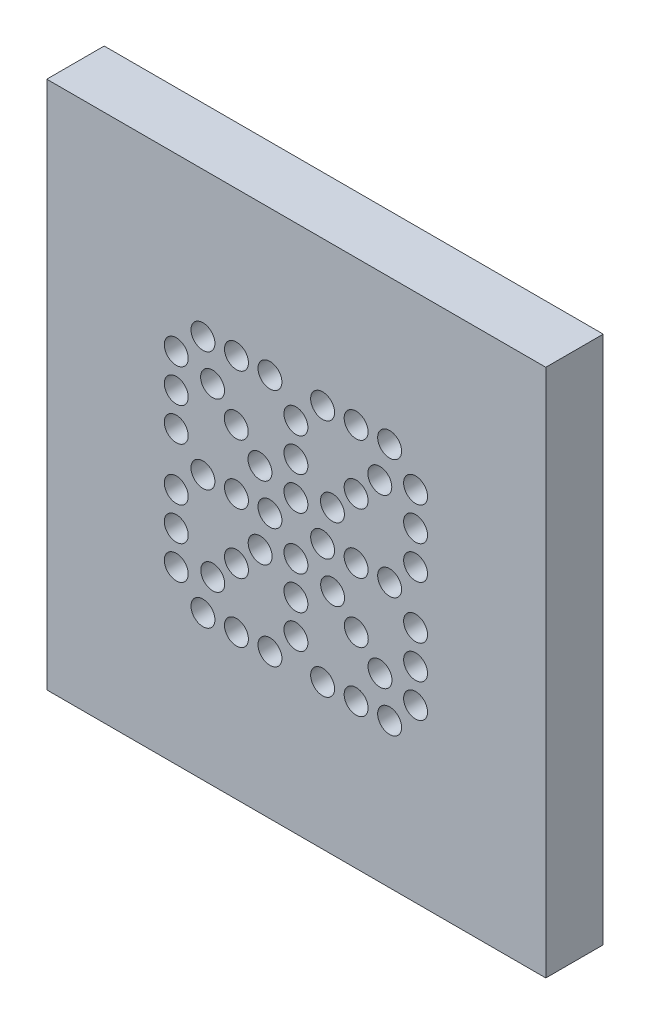
SolidWorks part; units mm, degrees
material "ABS PC"
ref_plane "Front Plane" through (0, 0, 0) normal (0, 0, 1) x (1, 0, 0)
ref_plane "Top Plane" through (0, 0, 0) normal (0, 1, 0) x (1, 0, 0)
ref_plane "Right Plane" through (0, 0, 0) normal (1, 0, 0) x (0, 0, -1)
sketch "Sketch1" plane through (0, 0, 0) normal (0, 0, 1) x (1, 0, 0)
  line L0 (265.9975, 197.0179) -> (342.1693, 194.9479) construction
  line L1 (297.418, 228.3826) -> (298.307, 228.3826) construction
  line L2 (297.418, 228.3826) -> (300.593, 228.3826) construction
  line L3 (302.371, 228.3826) -> (302.371, 231.5576) construction
  line L4 (296.7097, 229.0811) -> (296.7097, 229.9701) construction
  line L5 (296.7097, 230.8591) -> (296.7097, 234.0341) construction
  line L6 (296.7097, 234.0341) -> (299.8847, 234.0341) construction
  line L7 (296.7097, 234.0341) -> (297.0639, 234.3834) construction
  line L8 (296.7097, 234.0341) -> (297.418, 234.7326) construction
  line L9 (299.196, 231.5576) -> (300.593, 231.5576) construction
  line L10 (297.0639, 234.3834) -> (299.5404, 231.9069) construction
  line L11 (296.7097, 232.2561) -> (296.7097, 230.8591)
  line L12 (297.418, 231.5576) -> (296.7097, 231.5576) construction
  line L13 (299.8847, 232.2561) -> (299.196, 231.5576) construction
  line L14 (299.8945, 231.5576) -> (298.9307, 232.5165) construction
  line L15 (299.8945, 231.5576) -> (300.8534, 232.5214) construction
  line L16 (297.418, 234.7326) -> (307.578, 234.7326) construction
  line L17 (293.5347, 230.4146) -> (293.5347, 229.5256) construction
  line L18 (293.5347, 232.7006) -> (293.5347, 230.4146) construction
  line L19 (335.8892, 225.6039) -> (291.1852, 225.6039)
  line L20 (335.8892, 225.6039) -> (335.8892, 237.5114)
  line L21 (335.8892, 237.5114) -> (291.1852, 237.5114)
  line L22 (291.1852, 225.6039) -> (291.1852, 237.5114)
  line L23 (335.8892, 225.6039) -> (291.1852, 237.5114) construction
  line L24 (335.8892, 237.5114) -> (291.1852, 225.6039) construction
  line L25 (333.5397, 232.2561) -> (333.5397, 230.8591) construction
  line L26 (293.5347, 231.5576) -> (333.5397, 231.5576) construction
  circle A0 centre (297.418, 228.3826) radius 0.3175
  circle A3 centre (298.307, 228.3826) radius 0.3175
  circle A4 centre (299.196, 228.3826) radius 0.3175
  circle A5 centre (300.593, 228.3826) radius 0.3175
  circle A6 centre (301.482, 228.3826) radius 0.3175
  circle A7 centre (302.371, 228.3826) radius 0.3175
  circle A8 centre (302.371, 231.5576) radius 0.3175
  circle A9 centre (301.482, 231.5576) radius 0.3175
  circle A10 centre (300.593, 231.5576) radius 0.3175
  circle A11 centre (299.196, 231.5576) radius 0.3175
  circle A12 centre (298.307, 231.5576) radius 0.3175
  circle A13 centre (297.418, 231.5576) radius 0.3175
  circle A14 centre (302.371, 234.7326) radius 0.3175
  circle A15 centre (301.482, 234.7326) radius 0.3175
  circle A16 centre (300.593, 234.7326) radius 0.3175
  circle A17 centre (299.196, 234.7326) radius 0.3175
  circle A18 centre (298.307, 234.7326) radius 0.3175
  circle A19 centre (297.418, 234.7326) radius 0.3175
  circle A20 centre (296.7097, 229.0811) radius 0.3175
  circle A21 centre (296.7097, 229.9701) radius 0.3175
  circle A22 centre (296.7097, 230.8591) radius 0.3175
  circle A23 centre (296.7097, 234.0341) radius 0.3175
  circle A24 centre (296.7097, 233.1451) radius 0.3175
  circle A25 centre (296.7097, 232.2561) radius 0.3175
  circle A26 centre (299.8847, 234.0341) radius 0.3175
  circle A27 centre (299.8847, 233.1451) radius 0.3175
  circle A28 centre (299.8847, 232.2561) radius 0.3175
  circle A29 centre (299.8847, 230.8591) radius 0.3175
  circle A30 centre (299.8847, 229.9701) radius 0.3175
  circle A31 centre (299.8847, 229.0811) radius 0.3175
  circle A32 centre (297.6735, 233.7737) radius 0.3175
  circle A33 centre (298.3021, 233.1451) radius 0.3175
  circle A34 centre (298.9307, 232.5165) radius 0.3175
  circle A35 centre (303.0597, 234.0341) radius 0.3175
  circle A36 centre (303.0597, 233.1451) radius 0.3175
  circle A37 centre (303.0597, 232.2561) radius 0.3175
  circle A38 centre (303.0597, 230.8591) radius 0.3175
  circle A39 centre (303.0597, 229.9701) radius 0.3175
  circle A40 centre (303.0597, 229.0811) radius 0.3175
  circle A41 centre (300.8534, 232.5214) radius 0.3175
  circle A42 centre (301.482, 233.15) radius 0.3175
  circle A43 centre (302.1106, 233.7786) radius 0.3175
  circle A44 centre (300.8582, 230.5987) radius 0.3175
  circle A45 centre (301.4869, 229.9701) radius 0.3175
  circle A46 centre (302.1155, 229.3415) radius 0.3175
  circle A47 centre (298.9356, 230.5939) radius 0.3175
  circle A48 centre (298.307, 229.9653) radius 0.3175
  circle A49 centre (297.6784, 229.3366) radius 0.3175
  circle A50 centre (307.578, 234.7326) radius 0.3175
  circle A51 centre (306.8697, 234.0341) radius 0.3175
  circle A52 centre (306.8697, 233.1451) radius 0.3175
  circle A53 centre (306.8697, 232.2561) radius 0.3175
  circle A54 centre (308.467, 234.7326) radius 0.3175
  circle A55 centre (309.356, 234.7326) radius 0.3175
  circle A56 centre (310.753, 234.7326) radius 0.3175
  circle A57 centre (311.642, 234.7326) radius 0.3175
  circle A58 centre (312.531, 234.7326) radius 0.3175
  circle A59 centre (313.2197, 234.0341) radius 0.3175
  circle A60 centre (313.2197, 233.1451) radius 0.3175
  circle A61 centre (313.2197, 232.2561) radius 0.3175
  circle A62 centre (313.2197, 230.8591) radius 0.3175
  circle A63 centre (313.2197, 229.9701) radius 0.3175
  circle A64 centre (313.2197, 229.0811) radius 0.3175
  circle A65 centre (312.531, 228.3826) radius 0.3175
  circle A66 centre (311.642, 228.3826) radius 0.3175
  circle A67 centre (310.753, 228.3826) radius 0.3175
  circle A68 centre (309.356, 228.3826) radius 0.3175
  circle A69 centre (308.467, 228.3826) radius 0.3175
  circle A70 centre (307.578, 228.3826) radius 0.3175
  circle A71 centre (306.8697, 229.0811) radius 0.3175
  circle A72 centre (306.8697, 229.9701) radius 0.3175
  circle A73 centre (306.8697, 230.8591) radius 0.3175
  circle A74 centre (307.578, 231.5576) radius 0.3175
  circle A75 centre (308.467, 231.5576) radius 0.3175
  circle A76 centre (309.356, 231.5576) radius 0.3175
  circle A77 centre (310.753, 231.5576) radius 0.3175
  circle A78 centre (311.642, 231.5576) radius 0.3175
  circle A79 centre (312.531, 231.5576) radius 0.3175
  circle A80 centre (312.2706, 233.7786) radius 0.3175
  circle A81 centre (311.642, 233.15) radius 0.3175
  circle A82 centre (311.0134, 232.5214) radius 0.3175
  circle A83 centre (310.0447, 232.2561) radius 0.3175
  circle A84 centre (310.0447, 233.1451) radius 0.3175
  circle A85 centre (310.0447, 234.0341) radius 0.3175
  circle A86 centre (309.0907, 232.5165) radius 0.3175
  circle A87 centre (308.4621, 233.1451) radius 0.3175
  circle A88 centre (307.8335, 233.7737) radius 0.3175
  circle A89 centre (307.8384, 229.3366) radius 0.3175
  circle A90 centre (308.467, 229.9653) radius 0.3175
  circle A91 centre (309.0956, 230.5939) radius 0.3175
  circle A92 centre (310.0447, 230.8591) radius 0.3175
  circle A93 centre (310.0447, 229.9701) radius 0.3175
  circle A94 centre (310.0447, 229.0811) radius 0.3175
  circle A95 centre (312.2755, 229.3415) radius 0.3175
  circle A96 centre (311.6469, 229.9701) radius 0.3175
  circle A97 centre (311.0182, 230.5987) radius 0.3175
  circle A98 centre (317.738, 234.7326) radius 0.3175
  circle A99 centre (317.0297, 234.0341) radius 0.3175
  circle A100 centre (317.0297, 233.1451) radius 0.3175
  circle A101 centre (317.0297, 232.2561) radius 0.3175
  circle A102 centre (318.627, 234.7326) radius 0.3175
  circle A103 centre (319.516, 234.7326) radius 0.3175
  circle A104 centre (320.913, 234.7326) radius 0.3175
  circle A105 centre (321.802, 234.7326) radius 0.3175
  circle A106 centre (322.691, 234.7326) radius 0.3175
  circle A107 centre (323.3797, 234.0341) radius 0.3175
  circle A108 centre (323.3797, 233.1451) radius 0.3175
  circle A109 centre (323.3797, 232.2561) radius 0.3175
  circle A110 centre (323.3797, 230.8591) radius 0.3175
  circle A111 centre (323.3797, 229.9701) radius 0.3175
  circle A112 centre (323.3797, 229.0811) radius 0.3175
  circle A113 centre (322.691, 228.3826) radius 0.3175
  circle A114 centre (321.802, 228.3826) radius 0.3175
  circle A115 centre (320.913, 228.3826) radius 0.3175
  circle A116 centre (319.516, 228.3826) radius 0.3175
  circle A117 centre (318.627, 228.3826) radius 0.3175
  circle A118 centre (317.738, 228.3826) radius 0.3175
  circle A119 centre (317.0297, 229.0811) radius 0.3175
  circle A120 centre (317.0297, 229.9701) radius 0.3175
  circle A121 centre (317.0297, 230.8591) radius 0.3175
  circle A122 centre (317.738, 231.5576) radius 0.3175
  circle A123 centre (318.627, 231.5576) radius 0.3175
  circle A124 centre (319.516, 231.5576) radius 0.3175
  circle A125 centre (320.913, 231.5576) radius 0.3175
  circle A126 centre (321.802, 231.5576) radius 0.3175
  circle A127 centre (322.691, 231.5576) radius 0.3175
  circle A128 centre (322.4306, 233.7786) radius 0.3175
  circle A129 centre (321.802, 233.15) radius 0.3175
  circle A130 centre (321.1734, 232.5214) radius 0.3175
  circle A131 centre (320.2047, 232.2561) radius 0.3175
  circle A132 centre (320.2047, 233.1451) radius 0.3175
  circle A133 centre (320.2047, 234.0341) radius 0.3175
  circle A134 centre (319.2507, 232.5165) radius 0.3175
  circle A135 centre (318.6221, 233.1451) radius 0.3175
  circle A136 centre (317.9935, 233.7737) radius 0.3175
  circle A137 centre (317.9984, 229.3366) radius 0.3175
  circle A138 centre (318.627, 229.9653) radius 0.3175
  circle A139 centre (319.2556, 230.5939) radius 0.3175
  circle A140 centre (320.2047, 230.8591) radius 0.3175
  circle A141 centre (320.2047, 229.9701) radius 0.3175
  circle A142 centre (320.2047, 229.0811) radius 0.3175
  circle A143 centre (322.4355, 229.3415) radius 0.3175
  circle A144 centre (321.8069, 229.9701) radius 0.3175
  circle A145 centre (321.1782, 230.5987) radius 0.3175
  circle A146 centre (327.898, 234.7326) radius 0.3175
  circle A147 centre (327.1897, 234.0341) radius 0.3175
  circle A148 centre (327.1897, 233.1451) radius 0.3175
  circle A149 centre (327.1897, 232.2561) radius 0.3175
  circle A150 centre (328.787, 234.7326) radius 0.3175
  circle A151 centre (329.676, 234.7326) radius 0.3175
  circle A152 centre (331.073, 234.7326) radius 0.3175
  circle A153 centre (331.962, 234.7326) radius 0.3175
  circle A154 centre (332.851, 234.7326) radius 0.3175
  circle A155 centre (333.5397, 234.0341) radius 0.3175
  circle A156 centre (333.5397, 233.1451) radius 0.3175
  circle A157 centre (333.5397, 232.2561) radius 0.3175
  circle A158 centre (333.5397, 230.8591) radius 0.3175
  circle A159 centre (333.5397, 229.9701) radius 0.3175
  circle A160 centre (333.5397, 229.0811) radius 0.3175
  circle A161 centre (332.851, 228.3826) radius 0.3175
  circle A162 centre (331.962, 228.3826) radius 0.3175
  circle A163 centre (331.073, 228.3826) radius 0.3175
  circle A164 centre (329.676, 228.3826) radius 0.3175
  circle A165 centre (328.787, 228.3826) radius 0.3175
  circle A166 centre (327.898, 228.3826) radius 0.3175
  circle A167 centre (327.1897, 229.0811) radius 0.3175
  circle A168 centre (327.1897, 229.9701) radius 0.3175
  circle A169 centre (327.1897, 230.8591) radius 0.3175
  circle A170 centre (327.898, 231.5576) radius 0.3175
  circle A171 centre (328.787, 231.5576) radius 0.3175
  circle A172 centre (329.676, 231.5576) radius 0.3175
  circle A173 centre (331.073, 231.5576) radius 0.3175
  circle A174 centre (331.962, 231.5576) radius 0.3175
  circle A175 centre (332.851, 231.5576) radius 0.3175
  circle A176 centre (332.5906, 233.7786) radius 0.3175
  circle A177 centre (331.962, 233.15) radius 0.3175
  circle A178 centre (331.3334, 232.5214) radius 0.3175
  circle A179 centre (330.3647, 232.2561) radius 0.3175
  circle A180 centre (330.3647, 233.1451) radius 0.3175
  circle A181 centre (330.3647, 234.0341) radius 0.3175
  circle A182 centre (329.4107, 232.5165) radius 0.3175
  circle A183 centre (328.7821, 233.1451) radius 0.3175
  circle A184 centre (328.1535, 233.7737) radius 0.3175
  circle A185 centre (328.1584, 229.3366) radius 0.3175
  circle A186 centre (328.787, 229.9653) radius 0.3175
  circle A187 centre (329.4156, 230.5939) radius 0.3175
  circle A188 centre (330.3647, 230.8591) radius 0.3175
  circle A189 centre (330.3647, 229.9701) radius 0.3175
  circle A190 centre (330.3647, 229.0811) radius 0.3175
  circle A191 centre (332.5955, 229.3415) radius 0.3175
  circle A192 centre (331.9669, 229.9701) radius 0.3175
  circle A193 centre (331.3382, 230.5987) radius 0.3175
  circle A194 centre (293.5347, 229.5256) radius 0.3175
  circle A195 centre (293.5347, 230.4146) radius 0.3175
  circle A196 centre (293.5347, 233.5896) radius 0.3175
  circle A197 centre (293.5347, 232.7006) radius 0.3175
  point P81 (299.8945, 231.5576)
  point P96 (298.3021, 233.1451)
  point P410 (293.5347, 229.9701)
  point P411 (313.5372, 231.5576)
  point P422 (313.5372, 231.5576)
  dimension "D2" = 0.635
  dimension "D1" = 76.2
  dimension "D4" = 0.889
  dimension "D6" = 3.175
  dimension "D8" = 3.175
  dimension "D10" = 0.889
  dimension "D12" = 3.175
  dimension "D14" = 3.175
  dimension "D15" = 0.7082
  dimension "D16" = 0.889
  dimension "D17" = 0.889
  dimension "D19" = 90
  dimension "D20" = 1.3595
  dimension "D22" = 10.16
  dimension "D23" = 0.889
  dimension "D24" = 3.175
  dimension "D25" = 11.9075
  dimension "D26" = 44.704
  dimension "D3" = 3
  dimension "D5" = 2
  dimension "D7" = 3
  dimension "D9" = 3
  dimension "D11" = 2
  dimension "D13" = 3
  dimension "D21" = 4
  dimension "D18" = 4
extrude "Boss-Extrude1" add sketch "Sketch1" along normal blind 1.524 contours L22 L19 L20 L21 A196 A195 A194 A193 A192 A191 A190 A189 A188 A187 A186 A185 A184 A183 A182 A181 A180 A179 A178 A177 A176 A175 A174
pattern_linear "LPattern1" count 5 spacing 20.32 along (0, -1, 0) of "Boss-Extrude1"
sketch "Sketch2" plane through (0, 0, 1.524) normal (0, 0, 1) x (1, 0, 0)
  line L1 (291.1852, 217.1914) -> (335.8892, 217.1914)
  line L2 (291.1852, 217.1914) -> (291.1852, 225.6039)
  line L3 (291.1852, 225.6039) -> (335.8892, 225.6039)
  line L4 (335.8892, 217.1914) -> (335.8892, 225.6039)
  line L5 (291.1852, 196.8714) -> (335.8892, 196.8714)
  line L6 (291.1852, 196.8714) -> (291.1852, 205.2839)
  line L7 (291.1852, 205.2839) -> (335.8892, 205.2839)
  line L8 (335.8892, 196.8714) -> (335.8892, 205.2839)
  line L9 (291.1852, 176.5514) -> (335.8892, 176.5514)
  line L10 (291.1852, 176.5514) -> (291.1852, 184.9639)
  line L11 (291.1852, 184.9639) -> (335.8892, 184.9639)
  line L12 (335.8892, 176.5514) -> (335.8892, 184.9639)
  line L13 (291.1852, 156.2314) -> (335.8892, 156.2314)
  line L14 (291.1852, 156.2314) -> (291.1852, 164.6439)
  line L15 (291.1852, 164.6439) -> (335.8892, 164.6439)
  line L16 (335.8892, 156.2314) -> (335.8892, 164.6439)
  line L17 (291.1852, 237.5114) -> (335.8892, 237.5114)
  line L18 (291.1852, 237.5114) -> (291.1852, 238.7814)
  line L19 (291.1852, 238.7814) -> (335.8892, 238.7814)
  line L20 (335.8892, 237.5114) -> (335.8892, 238.7814)
  line L21 (291.1852, 144.3239) -> (335.8892, 144.3239)
  line L22 (291.1852, 144.3239) -> (291.1852, 143.0539)
  line L23 (291.1852, 143.0539) -> (335.8892, 143.0539)
  line L24 (335.8892, 144.3239) -> (335.8892, 143.0539)
  dimension "D1" = 1.27
extrude "Boss-Extrude2" add sketch "Sketch2" against normal up to surface (1.524 mm away) up to face at (297.0272, 230.8591, 0)
hole_wizard "#2 Clearance Hole1" positions "Sketch3" profile "Sketch4" hole size "#2" standard "ANSI Inch"
sketch "Sketch3" plane through (0, 0, 1.524) normal (0, 0, 1) x (1, 0, 0)
  point P0 (297.0272, 221.3983)
  point P3 (330.0472, 221.3983)
  point P6 (330.0472, 201.0783)
  point P9 (297.0272, 201.0783)
  point P12 (297.0272, 180.7583)
  point P15 (330.0472, 180.7583)
  point P18 (330.0472, 160.4383)
  point P21 (297.0272, 160.4383)
sketch "Sketch4" plane through (297.0272, 221.3983, 1.524) normal (1, 0, 0) x (0, -1, 0)
  line L0 (0, 0) -> (0, 1.524)
  line L1 (0, 1.524) -> (1.3525, 1.524)
  line L2 (1.3525, 1.524) -> (1.3525, 0)
  line L5 (1.3525, 0) -> (0, 0)
  line L11 (0, -6.35) -> (0, 107.95) construction
  dimension "Thru Hole Dia." = 2.7051
  dimension "Thru Hole Depth" = 1.524
sketch "Sketch5" plane through (0, 0, 1.524) normal (0, 0, 1) x (1, 0, 0)
  line L0 (313.594, 238.5744) -> (326.835, 224.5409) construction
  line L1 (313.594, 238.5744) -> (326.835, 238.5744)
  line L2 (313.594, 238.5744) -> (313.594, 224.5409)
  line L3 (313.594, 224.5409) -> (326.835, 224.5409)
  line L4 (291.1852, 238.7814) -> (291.1852, 143.0539)
  line L5 (291.1852, 143.0539) -> (335.8892, 143.0539)
  line L6 (335.8892, 143.0539) -> (335.8892, 238.7814)
  line L7 (335.8892, 238.7814) -> (291.1852, 238.7814)
  line L8 (291.1852, 238.7814) -> (291.1852, 143.0539)
  line L9 (291.1852, 143.0539) -> (335.8892, 143.0539)
  line L10 (335.8892, 143.0539) -> (335.8892, 238.7814)
  line L11 (335.8892, 238.7814) -> (291.1852, 238.7814)
  line L12 (326.835, 238.5744) -> (326.835, 224.5409)
  line L13 (329.676, 231.5576) -> (331.073, 231.5576) construction
  line L14 (319.516, 231.5576) -> (320.913, 231.5576) construction
  point P8 (320.2145, 231.5576)
  dimension "D2" = 13.241
  dimension "D3" = 14.0335
  dimension "D1" = 0
extrude "Cut-Extrude2" cut sketch "Sketch5" against normal through all contours L10 L11 L8 L9 L1 L12 L3 L2
